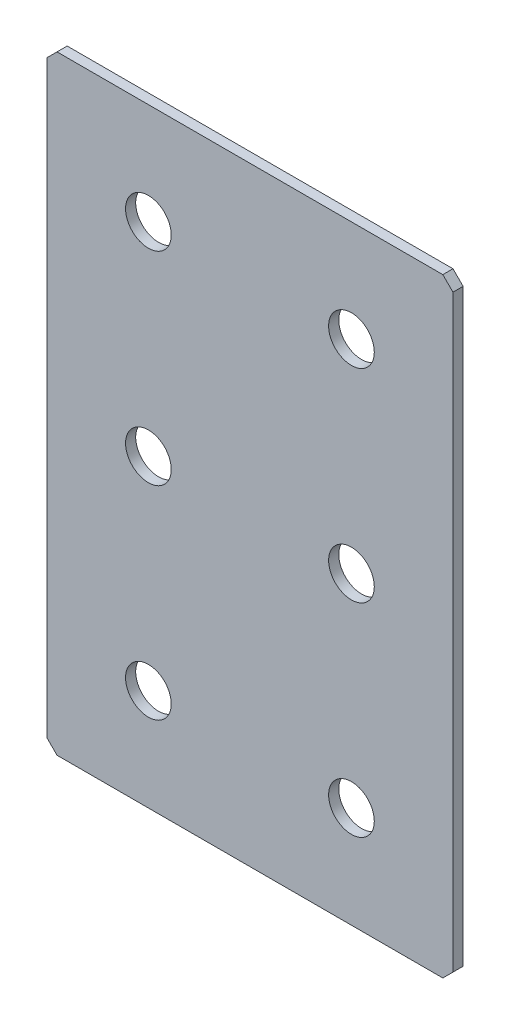
SolidWorks part; units mm, degrees
material "Простая углеродистая сталь"
ref_plane "Спереди(Плоскость XY)" through (0, 0, 0) normal (0, 0, 1) x (1, 0, 0)
ref_plane "Сверху(Плоскость XZ)" through (0, 0, 0) normal (0, 1, 0) x (1, 0, 0)
ref_plane "Справа(Плоскость ZY)" through (0, 0, 0) normal (1, 0, 0) x (0, 0, -1)
sketch "Эскиз1" plane through (0, 0, 0) normal (0, 0, 1) x (1, 0, 0)
  line L1 (-40, -60) -> (40, -60)
  line L2 (-40, -60) -> (-40, 60)
  line L3 (-40, 60) -> (40, 60)
  line L4 (40, -60) -> (40, 60)
  line L5 (-40, -60) -> (40, 60) construction
  line L6 (-40, 60) -> (40, -60) construction
  point P0 (0, 0)
  dimension "D1" = 80
  dimension "D2" = 120
extrude "Бобышка-Вытянуть1" add sketch "Эскиз1" along normal blind 2
chamfer "Фаска1" distance 2 angle 45 4 edges at (-40, -60, 1) (40, -60, 1) (-40, 60, 1) (40, 60, 1)
hole_wizard "Отверстие с зазором M81" positions "Эскиз2" profile "Эскиз3" hole size "M8" standard "DIN" end condition through all
sketch "Эскиз2" plane through (0, 0, 2) normal (0, 0, 1) x (1, 0, 0)
  line L0 (-20, 0) -> (20, 0) construction
  line L1 (20, 0) -> (20, 40) construction
  line L3 (20, 0) -> (20, -40) construction
  line L5 (-20, 0) -> (-20, 40) construction
  line L7 (-20, 0) -> (-20, -40) construction
  point P0 (-20, 40)
  point P2 (20, 40)
  point P4 (20, 0)
  point P6 (-20, 0)
  point P8 (-20, -40)
  point P10 (20, -40)
  dimension "D1" = 40
sketch "Эскиз3" plane through (-20, 40, 2) normal (1, 0, 0) x (0, -1, 0)
  line L0 (0, 0) -> (0, 2)
  line L1 (0, 2) -> (4.5, 2)
  line L2 (4.5, 2) -> (4.5, 0)
  line L5 (4.5, 0) -> (0, 0)
  line L11 (0, -6.35) -> (0, 107.95) construction
  dimension "Диаметр сквозного отверстия" = 9
  dimension "Глубина сквозного отверстия" = 2
